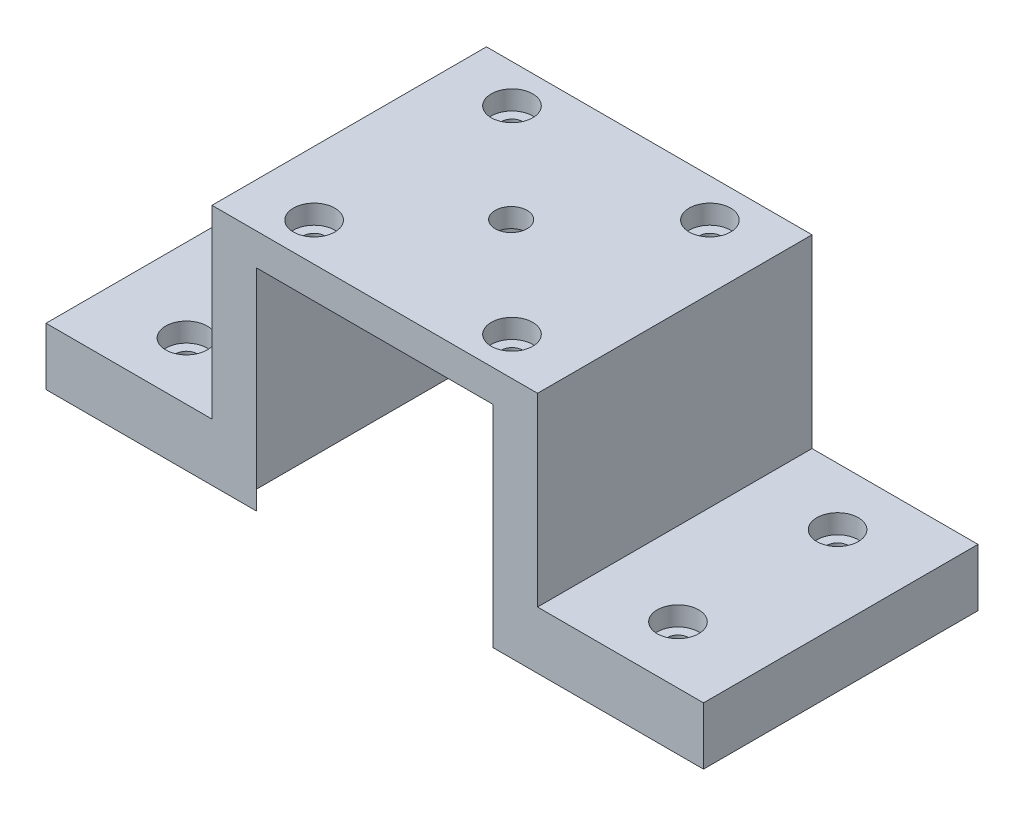
SolidWorks part; units mm, degrees
ref_plane "Front" through (0, 0, 0) normal (0, 0, 1) x (1, 0, 0)
ref_plane "Top" through (0, 0, 0) normal (0, 1, 0) x (1, 0, 0)
ref_plane "Right" through (0, 0, 0) normal (1, 0, 0) x (0, 0, -1)
sketch "Sketch1" plane through (0, 0, 0) normal (0, 0, 1) x (1, 0, 0)
  line L0 (-51.3691, 0) -> (-21.3691, 0)
  line L1 (-21.3691, 0) -> (-21.3691, 33)
  line L2 (21.6309, 33) -> (21.6309, 0)
  line L3 (21.6309, 0) -> (51.6309, 0)
  line L4 (51.6309, 0) -> (51.6309, 9)
  line L5 (51.6309, 9) -> (25.6309, 9)
  line L6 (25.6309, 9) -> (25.6309, 38)
  line L7 (25.6309, 38) -> (-25.3691, 38)
  line L8 (-25.3691, 38) -> (-25.3691, 9)
  line L9 (-25.3691, 9) -> (-51.3691, 9)
  line L10 (-51.3691, 9) -> (-51.3691, 0)
  line L11 (-21.3691, 33) -> (21.6309, 33)
  dimension "D1" = 43
  dimension "D2" = 4
  dimension "D3" = 4
  dimension "D4" = 9
  dimension "D5" = 9
  dimension "D6" = 33
  dimension "D7" = 5
  dimension "D8" = 30
  dimension "D9" = 30
extrude "Boss-Extrude1" add sketch "Sketch1" along normal blind 43
sketch "Sketch5" plane through (0, 33, 0) normal (0, -1, 0) x (1, 0, 0)
  line L0 (-21.3691, 43) -> (-18.3691, 43)
  line L1 (-21.3691, 43) -> (21.6309, 43) construction
  line L2 (-18.3691, 43) -> (-21.3691, 40)
  line L3 (-21.3691, 43) -> (-21.3691, 0) construction
  line L4 (-21.3691, 40) -> (-21.3691, 43)
  line L5 (21.6309, 40) -> (21.6309, 43)
  line L6 (21.6309, 43) -> (21.6309, 0) construction
  line L7 (21.6309, 43) -> (18.6309, 43)
  line L8 (18.6309, 43) -> (21.6309, 40)
  line L9 (18.6309, 0) -> (21.6309, 0)
  line L10 (-21.3691, 0) -> (21.6309, 0) construction
  line L11 (21.6309, 0) -> (21.6309, 3)
  line L12 (21.6309, 3) -> (18.6309, 0)
  line L13 (-18.3691, 0) -> (-21.3691, 0)
  line L14 (-21.3691, 0) -> (-21.3691, 3)
  line L15 (-21.3691, 3) -> (-18.3691, 0)
  dimension "D1" = 3
  dimension "D2" = 3
  dimension "D3" = 3
  dimension "D4" = 3
  dimension "D5" = 3
  dimension "D6" = 3
  dimension "D7" = 3
  dimension "D8" = 3
extrude "Boss-Extrude2" add sketch "Sketch5" along normal blind 33
sketch "Sketch6" plane through (0, 33, 0) normal (0, -1, 0) x (1, 0, 0)
  circle A0 centre (0, 21.5) radius 11
  dimension "D1" = 22
extrude "Cut-Extrude1" cut sketch "Sketch6" against normal blind 2
sketch "Sketch7" plane through (0, 35, 0) normal (0, -1, 0) x (1, 0, 0)
  circle A0 centre (0, 21.5) radius 2.5
  dimension "D1" = 5
extrude "Cut-Extrude2" cut sketch "Sketch7" against normal through all
hole_wizard "CBORE for M3 SHCS1" positions "Sketch11" profile "Sketch12" counterbore size "M3" standard "ANSI Metric" end condition through all
sketch "Sketch11" plane through (0, 38, 0) normal (0, 1, 0) x (1, 0, 0)
  line L0 (25.6309, 0) -> (-25.3691, 0) construction
  circle A0 centre (0, -21.5) radius 2.5 construction
  point P0 (-15.3691, -6)
  point P2 (-15.3691, -37)
  point P4 (15.6309, -37)
  point P6 (15.6309, -6)
  point P12 (0.1309, 0)
  dimension "D1" = 15.5
  dimension "D2" = 15.5
  dimension "D3" = 15.5
  dimension "D4" = 15.5
sketch "Sketch12" plane through (-15.3691, 38, 6) normal (1, 0, 0) x (0, 0, 1)
  line L0 (0, 0) -> (0, 38)
  line L1 (0, 38) -> (1.7, 38)
  line L3 (1.7, 38) -> (1.7, 3)
  line L4 (1.7, 3) -> (3.25, 3)
  line L5 (3.25, 3) -> (3.25, 0)
  line L7 (3.25, 0) -> (0, 0)
  line L11 (0, -6.35) -> (0, 107.95) construction
  dimension "Thru Hole Dia." = 3.4
  dimension "Thru Hole Depth" = 38
  dimension "C'Bore Dia." = 6.5
  dimension "C'Bore Depth" = 3
hole_wizard "CBORE for M3 SHCS2" positions "Sketch13" profile "Sketch14" counterbore size "M3" standard "ANSI Metric" end condition through all
sketch "Sketch13" plane through (0, 9, 0) normal (0, 1, 0) x (1, 0, 0)
  line L0 (-51.3691, -43) -> (-51.3691, 0) construction
  line L1 (-25.3691, -43) -> (-51.3691, -43) construction
  line L2 (-25.3691, 0) -> (-51.3691, 0) construction
  point P0 (-38.3691, -9)
  point P2 (-38.3691, -34)
  dimension "D1" = 13
  dimension "D2" = 9
  dimension "D3" = 9
sketch "Sketch14" plane through (-38.3691, 9, 9) normal (1, 0, 0) x (0, 0, 1)
  line L0 (0, 0) -> (0, 9)
  line L1 (0, 9) -> (1.7, 9)
  line L3 (1.7, 9) -> (1.7, 3)
  line L4 (1.7, 3) -> (3.25, 3)
  line L5 (3.25, 3) -> (3.25, 0)
  line L7 (3.25, 0) -> (0, 0)
  line L11 (0, -6.35) -> (0, 107.95) construction
  dimension "Thru Hole Dia." = 3.4
  dimension "Thru Hole Depth" = 9
  dimension "C'Bore Dia." = 6.5
  dimension "C'Bore Depth" = 3
hole_wizard "CBORE for M3 SHCS3" positions "Sketch15" profile "Sketch16" counterbore size "M3" standard "ANSI Metric" end condition through all
sketch "Sketch15" plane through (0, 9, 0) normal (0, 1, 0) x (1, 0, 0)
  line L0 (51.6309, 0) -> (25.6309, 0) construction
  line L1 (51.6309, -43) -> (25.6309, -43) construction
  line L2 (51.6309, -43) -> (51.6309, 0) construction
  point P0 (38.6309, -34)
  point P2 (38.6309, -9)
  point P10 (38.6309, -43)
  dimension "D1" = 9
  dimension "D2" = 9
  dimension "D3" = 13
sketch "Sketch16" plane through (38.6309, 9, 34) normal (1, 0, 0) x (0, 0, 1)
  line L0 (0, 0) -> (0, 9)
  line L1 (0, 9) -> (1.7, 9)
  line L3 (1.7, 9) -> (1.7, 3)
  line L4 (1.7, 3) -> (3.25, 3)
  line L5 (3.25, 3) -> (3.25, 0)
  line L7 (3.25, 0) -> (0, 0)
  line L11 (0, -6.35) -> (0, 107.95) construction
  dimension "Thru Hole Dia." = 3.4
  dimension "Thru Hole Depth" = 9
  dimension "C'Bore Dia." = 6.5
  dimension "C'Bore Depth" = 3
